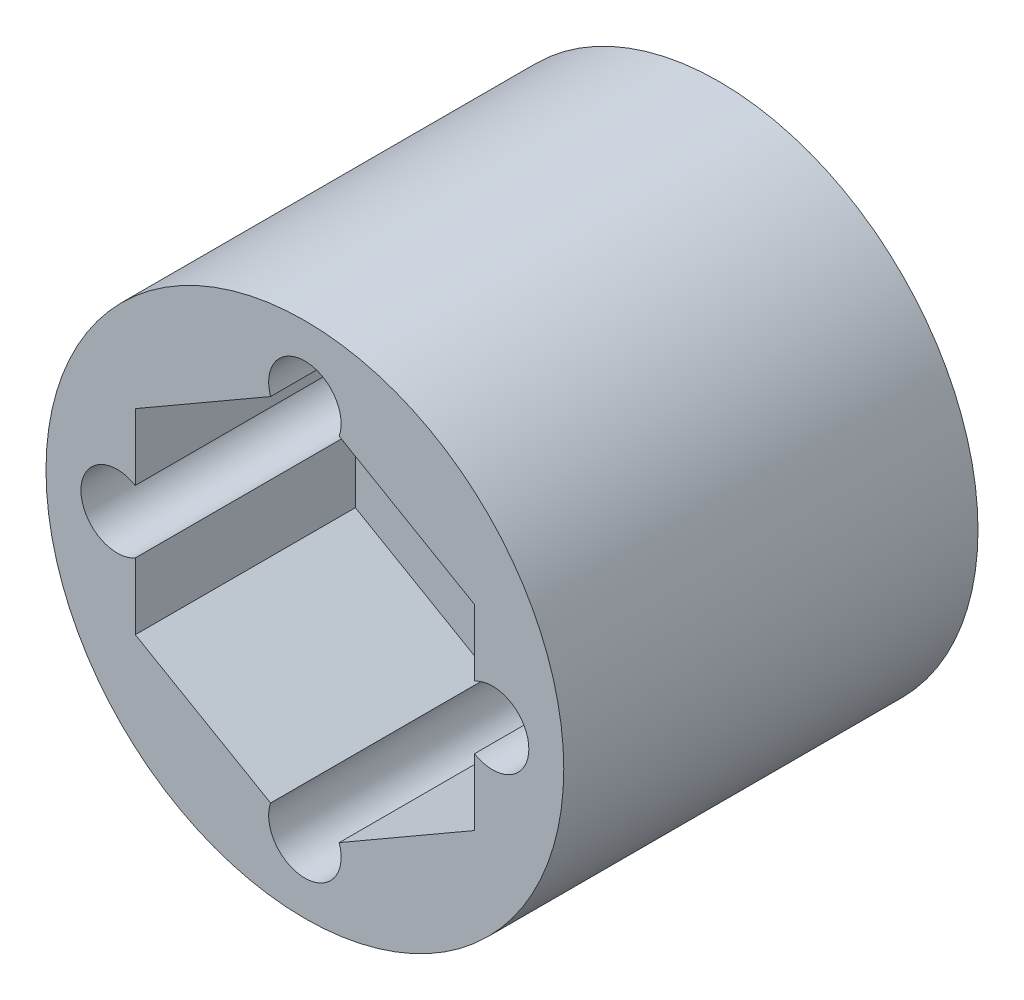
SolidWorks part; units mm, degrees
ref_plane "Front Plane" through (0, 0, 0) normal (0, 0, 1) x (1, 0, 0)
ref_plane "Top Plane" through (0, 0, 0) normal (0, 1, 0) x (1, 0, 0)
ref_plane "Right Plane" through (0, 0, 0) normal (1, 0, 0) x (0, 0, -1)
sketch "Sketch1" plane through (0, 0, 0) normal (0, 0, 1) x (1, 0, 0)
  line L0 (0, 0) -> (0, 12.391) construction
  circle A0 centre (0, 0) radius 10
  circle A1 centre (0, 7.25) radius 1.4
  circle A2 centre (0, 0) radius 4.25
  circle A3 centre (7.25, 0) radius 1.4
  circle A4 centre (0, -7.25) radius 1.4
  circle A5 centre (-7.25, 0) radius 1.4
  dimension "D1" = 20
  dimension "D2" = 2.8
  dimension "D4" = 8.5
  dimension "D3" = 7.25
  dimension "D5" = 4
extrude "Boss-Extrude1" add sketch "Sketch1" along normal blind 16
sketch "Sketch2" plane through (0, 0, 16) normal (0, 0, 1) x (1, 0, 0)
  line L1 (0, 7.5633) -> (-6.55, 3.7816)
  line L2 (-6.55, 3.7816) -> (-6.55, -3.7816)
  line L3 (-6.55, -3.7816) -> (0, -7.5633)
  line L4 (0, -7.5633) -> (6.55, -3.7816)
  line L5 (6.55, -3.7816) -> (6.55, 3.7816)
  line L6 (6.55, 3.7816) -> (0, 7.5633)
  circle A0 centre (0, 0) radius 6.55 construction
  dimension "D1" = 13.1
extrude "Cut-Extrude1" cut sketch "Sketch2" against normal blind 8.5
